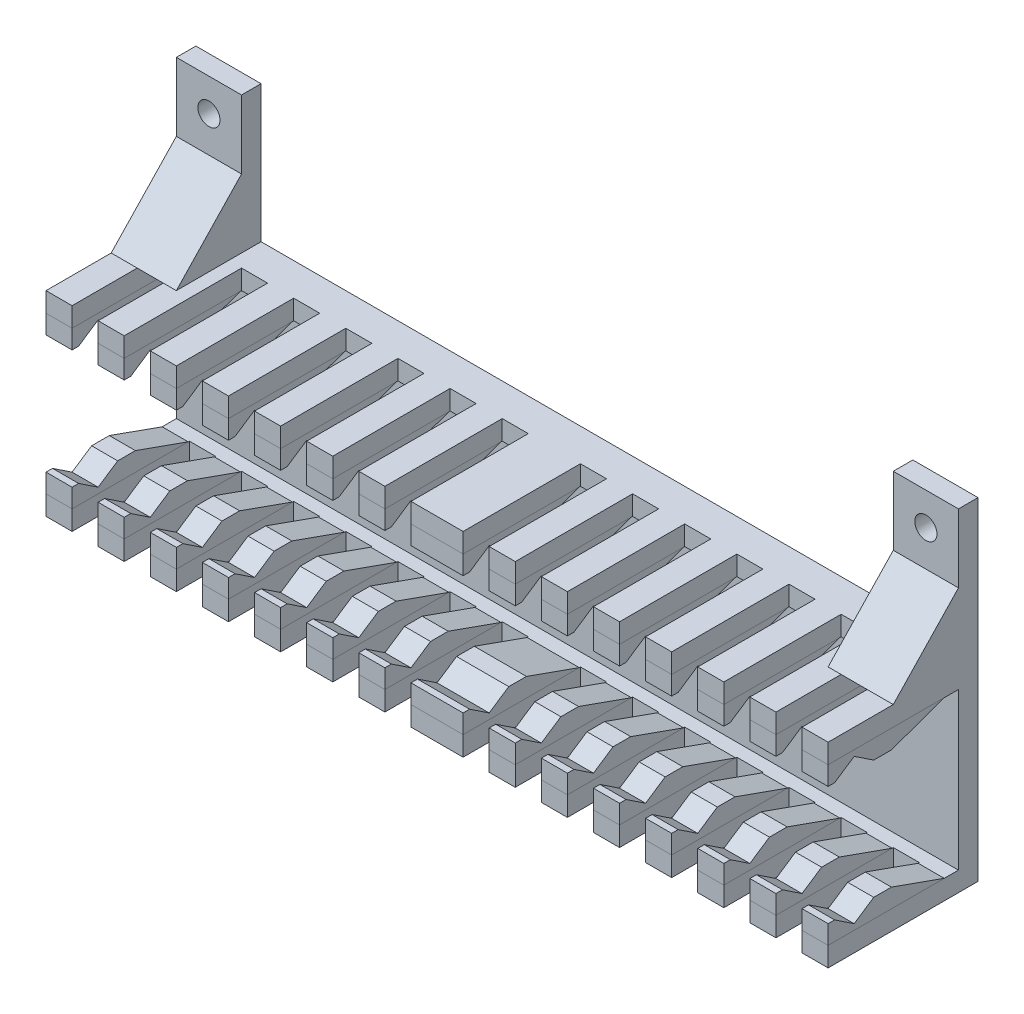
SolidWorks part; units mm, degrees
ref_plane "Plan de face" through (0, 0, 0) normal (0, 0, 1) x (1, 0, 0)
ref_plane "Plan de dessus" through (0, 0, 0) normal (0, 1, 0) x (1, 0, 0)
ref_plane "Plan de droite" through (0, 0, 0) normal (1, 0, 0) x (0, 0, -1)
sketch "Esquisse1" plane through (0, 0, 0) normal (0, 0, 1) x (1, 0, 0)
  line L0 (60, 30) -> (60, 0) construction
  line L1 (0, 0) -> (120, 0) construction
  line L2 (0, 0) -> (0, 30) construction
  line L3 (10, 30) -> (120, 30) construction
  line L4 (120, 0) -> (120, 30) construction
  line L5 (0, 0) -> (0, 51)
  line L6 (0, 30) -> (10, 30) construction
  line L7 (0, 30) -> (0, 51) construction
  line L8 (0, 51) -> (10, 51) construction
  line L9 (10, 30) -> (10, 51) construction
  line L10 (0, 51) -> (10, 51)
  line L11 (10, 51) -> (10, 30)
  line L12 (10, 30) -> (110, 30)
  line L13 (0, 0) -> (120, 0)
  line L14 (110, 51) -> (110, 30)
  line L15 (120, 0) -> (120, 51)
  line L16 (120, 51) -> (110, 51)
  circle A0 centre (5, 46) radius 1.7
  circle A1 centre (115, 46) radius 1.7 construction
  circle A2 centre (115, 46) radius 1.7
  dimension "D3" = 55
  dimension "D4" = 16
  dimension "D1" = 120
  dimension "D2" = 30
  dimension "D5" = 10
  dimension "D6" = 21
extrude "Boss.-Extru.1" add sketch "Esquisse1" along normal blind 3
sketch "Esquisse2" plane through (0, 0, 3) normal (0, 0, 1) x (1, 0, 0)
  line L0 (60, 15) -> (66.85, 15) construction
  line L1 (0, 0) -> (120, 0)
  line L2 (0, 0) -> (0, 3)
  line L3 (0, 3) -> (120, 3)
  line L4 (120, 0) -> (120, 3)
  line L5 (120, 30) -> (120, 27)
  line L6 (0, 27) -> (120, 27)
  line L7 (0, 30) -> (0, 27)
  line L8 (0, 30) -> (120, 30)
  line L48 (60, 30) -> (60, 0) construction
  line L49 (110, 30) -> (10, 30) construction
  line L50 (0, 0) -> (120, 0) construction
  dimension "D1" = 3
  dimension "D2" = 120
extrude "Boss.-Extru.2" add sketch "Esquisse2" along normal blind 20
sketch "Esquisse5" plane through (120, 0, 0) normal (1, 0, 0) x (0, 0, -1)
  line L0 (-23, 3) -> (-23, 5.884)
  line L1 (-23, 5.884) -> (-13.2851, 5.884)
  line L2 (-13.2851, 5.884) -> (-5.1785, 3)
  line L3 (-23, 3) -> (-3, 3) construction
  line L4 (-23, 3) -> (-5.1785, 3)
  line L5 (-3, 15) -> (-27.8564, 15) construction
  line L6 (-3, 3) -> (-3, 27) construction
  line L7 (-23, 27) -> (-5.1785, 27)
  line L8 (-13.2851, 24.116) -> (-5.1785, 27)
  line L9 (-23, 24.116) -> (-13.2851, 24.116)
  line L10 (-23, 27) -> (-23, 24.116)
extrude "Boss.-Extru.3" add sketch "Esquisse5" against normal blind 120 separate body
sketch "Esquisse6" plane through (120, 0, 0) normal (1, 0, 0) x (0, 0, -1)
  line L0 (-13.2851, 5.884) -> (-23, 5.884) construction
  line L1 (-19, 3.884) -> (-16, 5.884)
  line L2 (-22, 24.116) -> (-19, 26.116)
  line L3 (-19, 26.116) -> (-16, 24.116)
  line L4 (-23, 5.884) -> (-22, 5.884) construction
  line L5 (-22, 5.884) -> (-19, 3.884)
  line L6 (-22, 5.884) -> (-16, 5.884)
  line L7 (-3, 15) -> (-12.6037, 15) construction
  line L8 (-3, 3) -> (-3, 27) construction
  line L9 (-22, 24.116) -> (-16, 24.116)
  dimension "D1" = 1
  dimension "D2" = 2
  dimension "D3" = 3
  dimension "D4" = 3
extrude "Enlèv. mat.-Extru.1" cut sketch "Esquisse6" against normal blind 120
sketch "Esquisse7" plane through (0, 0, 0) normal (0, -1, 0) x (1, 0, 0)
  line L0 (60, 0) -> (60, 23) construction
  line L1 (0, 0) -> (120, 0) construction
  line L3 (0, 23) -> (120, 23) construction
  line L4 (56, 23) -> (52, 23)
  line L5 (56, 23) -> (56, 5)
  line L6 (56, 5) -> (52, 5)
  line L7 (52, 23) -> (52, 5)
  line L8 (48, 23) -> (44, 23)
  line L9 (48, 23) -> (48, 5)
  line L10 (48, 5) -> (44, 5)
  line L11 (44, 23) -> (44, 5)
  line L12 (40, 23) -> (36, 23)
  line L13 (40, 23) -> (40, 5)
  line L14 (40, 5) -> (36, 5)
  line L15 (36, 23) -> (36, 5)
  line L16 (32, 23) -> (28, 23)
  line L17 (32, 23) -> (32, 5)
  line L18 (32, 5) -> (28, 5)
  line L19 (28, 23) -> (28, 5)
  line L20 (24, 23) -> (20, 23)
  line L21 (24, 23) -> (24, 5)
  line L22 (24, 5) -> (20, 5)
  line L23 (20, 23) -> (20, 5)
  line L24 (16, 23) -> (12, 23)
  line L25 (16, 23) -> (16, 5)
  line L26 (16, 5) -> (12, 5)
  line L27 (12, 23) -> (12, 5)
  line L28 (8, 23) -> (4, 23)
  line L29 (8, 23) -> (8, 5)
  line L30 (8, 5) -> (4, 5)
  line L31 (4, 23) -> (4, 5)
  line L32 (116, 23) -> (116, 5)
  line L33 (112, 5) -> (116, 5)
  line L34 (112, 23) -> (112, 5)
  line L35 (112, 23) -> (116, 23)
  line L36 (108, 23) -> (108, 5)
  line L37 (104, 5) -> (108, 5)
  line L38 (104, 23) -> (104, 5)
  line L39 (104, 23) -> (108, 23)
  line L40 (100, 23) -> (100, 5)
  line L41 (96, 5) -> (100, 5)
  line L42 (96, 23) -> (96, 5)
  line L43 (96, 23) -> (100, 23)
  line L44 (92, 23) -> (92, 5)
  line L45 (88, 5) -> (92, 5)
  line L46 (88, 23) -> (88, 5)
  line L47 (88, 23) -> (92, 23)
  line L48 (84, 23) -> (84, 5)
  line L49 (80, 5) -> (84, 5)
  line L50 (80, 23) -> (80, 5)
  line L51 (80, 23) -> (84, 23)
  line L52 (76, 23) -> (76, 5)
  line L53 (72, 5) -> (76, 5)
  line L54 (72, 23) -> (72, 5)
  line L55 (72, 23) -> (76, 23)
  line L56 (68, 23) -> (68, 5)
  line L57 (64, 5) -> (68, 5)
  line L58 (64, 23) -> (64, 5)
  line L59 (64, 23) -> (68, 23)
  dimension "D1" = 18
  dimension "D2" = 4
  dimension "D3" = 4
  dimension "D4" = 7
extrude "Enlèv. mat.-Extru.2" cut sketch "Esquisse7" against normal blind 34
sketch "Esquisse8" plane through (120, 0, 0) normal (1, 0, 0) x (0, 0, -1)
  line L0 (-3, 30) -> (-13, 30)
  line L1 (-23, 30) -> (-3, 30) construction
  line L2 (-13, 30) -> (-3, 40.5)
  line L3 (-3, 30) -> (-3, 51) construction
  line L4 (-3, 40.5) -> (-3, 30)
extrude "Boss.-Extru.4" add sketch "Esquisse8" against normal blind 10
sketch "Esquisse9" plane through (0, 0, 0) normal (-1, 0, 0) x (0, 0, 1)
  line L0 (3, 40.5) -> (13, 30)
  line L1 (3, 51) -> (3, 30) construction
  line L2 (23, 30) -> (3, 30) construction
  line L3 (13, 30) -> (3, 30)
  line L4 (3, 30) -> (3, 40.5)
extrude "Boss.-Extru.5" add sketch "Esquisse9" against normal blind 10
